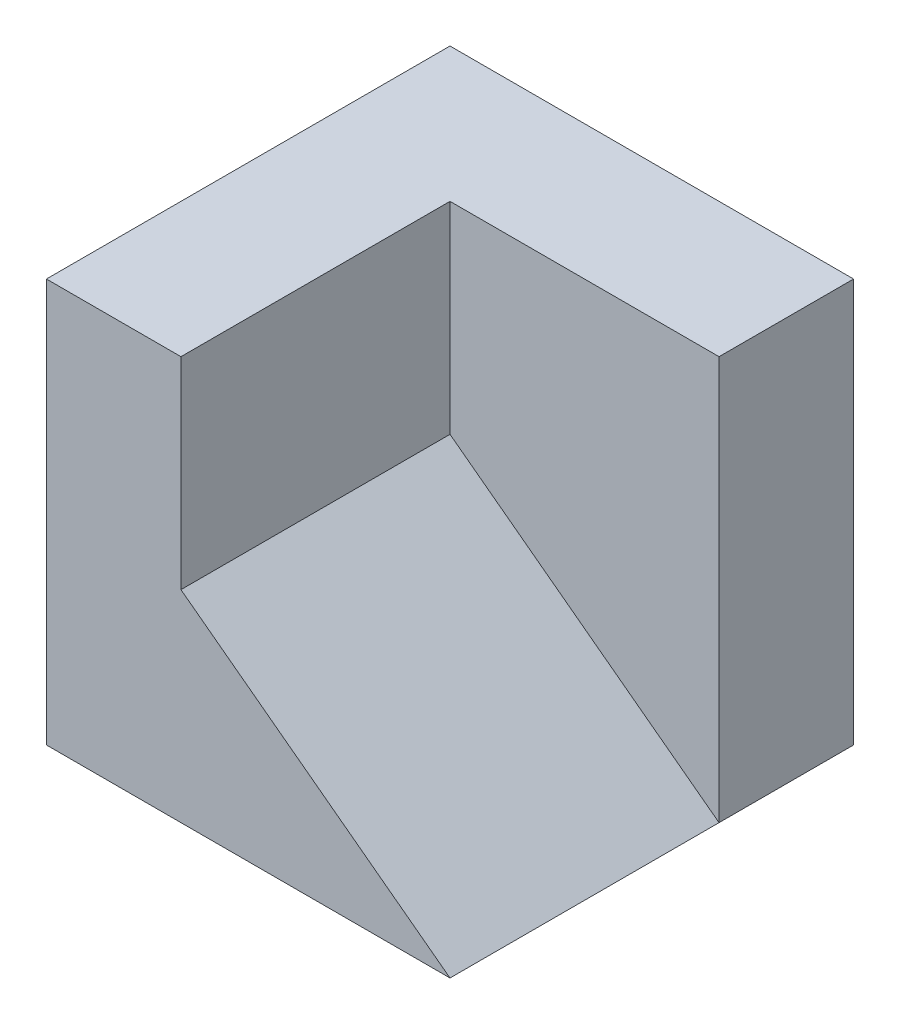
SolidWorks part; units mm, degrees
ref_plane "Alzado" through (0, 0, 0) normal (0, 0, 1) x (1, 0, 0)
ref_plane "Planta" through (0, 0, 0) normal (0, 1, 0) x (1, 0, 0)
ref_plane "Vista lateral" through (0, 0, 0) normal (1, 0, 0) x (0, 0, -1)
sketch "Croquis2" plane through (0, 0, 0) normal (0, 1, 0) x (1, 0, 0)
  line L0 (0, 0) -> (60, 0)
  line L1 (60, 0) -> (60, 60)
  line L2 (60, 60) -> (0, 60)
  line L3 (0, 60) -> (0, 0)
  point P5 (0, 0.3985)
  dimension "D1" = 60
extrude "Saliente-Extruir1" add sketch "Croquis2" along normal blind 60 contours L3 L0 L1 L2
sketch "Croquis3" plane through (0, 0, 0) normal (0, 0, 1) x (1, 0, 0)
  line L0 (60, 0) -> (20, 30)
  line L1 (20, 30) -> (20, 60)
  line L2 (0, 60) -> (60, 60) construction
  line L3 (20, 60) -> (60, 60)
  line L4 (60, 60) -> (60, 0) construction
  line L5 (60, 60) -> (60, 0)
  line L6 (0, 60) -> (0, 0) construction
  line L7 (0, 0) -> (60, 0) construction
  dimension "D1" = 20
  dimension "D2" = 30
extrude "Cortar-Extruir1" cut sketch "Croquis3" against normal blind 40
